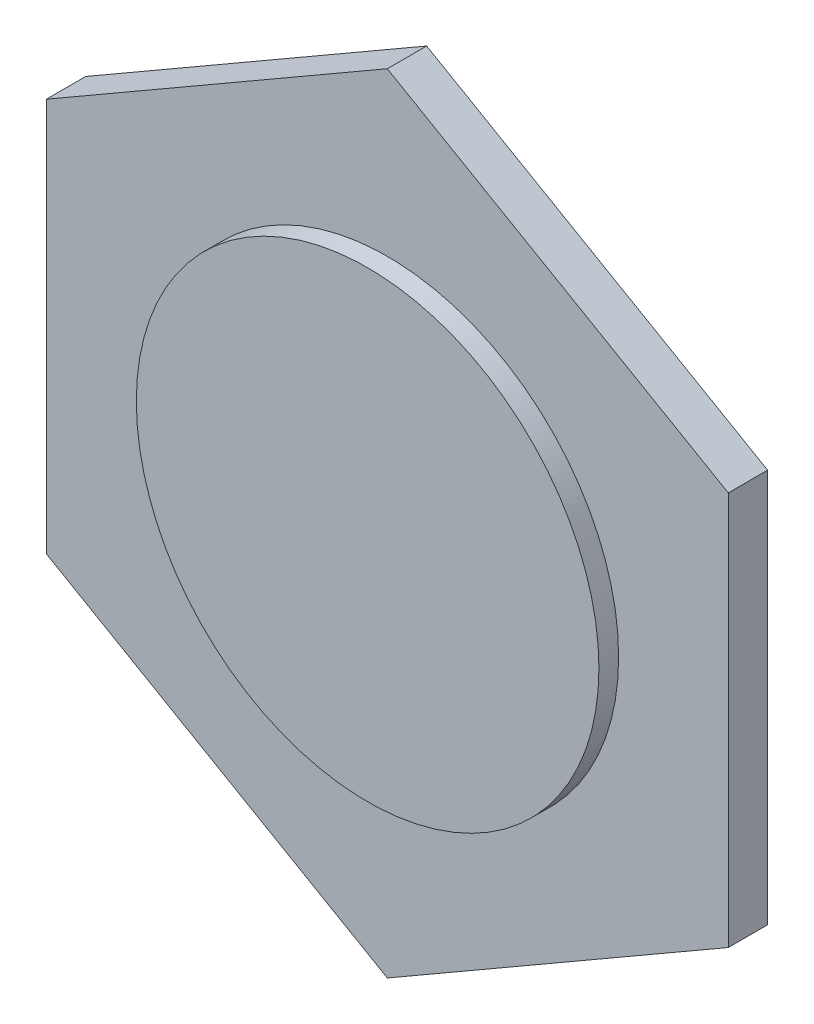
SolidWorks part; units mm, degrees
material "Nylon 101"
ref_plane "Front Plane" through (0, 0, 0) normal (0, 0, 1) x (1, 0, 0)
ref_plane "Top Plane" through (0, 0, 0) normal (0, 1, 0) x (1, 0, 0)
ref_plane "Right Plane" through (0, 0, 0) normal (1, 0, 0) x (0, 0, -1)
sketch "Sketch1" plane through (0, 0, 0) normal (0, 0, 1) x (1, 0, 0)
  line L1 (34.641, 20) -> (0, 40)
  line L2 (0, 40) -> (-34.641, 20)
  line L3 (-34.641, 20) -> (-34.641, -20)
  line L4 (-34.641, -20) -> (0, -40)
  line L5 (0, -40) -> (34.641, -20)
  line L6 (34.641, -20) -> (34.641, 20)
  circle A0 centre (0, 0) radius 23.5
  circle A1 centre (0, 0) radius 34.641 construction
  point P2 (0, 0)
  point P11 (0, 0)
  dimension "D1" = 47
  dimension "D2" = 40
extrude "Boss-Extrude1" add sketch "Sketch1" along normal blind 4
sketch "Sketch2" plane through (0, 0, 0) normal (0, 0, 1) x (1, 0, 0)
  circle A0 centre (0, 0) radius 23.5 construction
  circle A1 centre (0, 0) radius 23.5
extrude "Boss-Extrude2" add sketch "Sketch2" along normal blind 6
